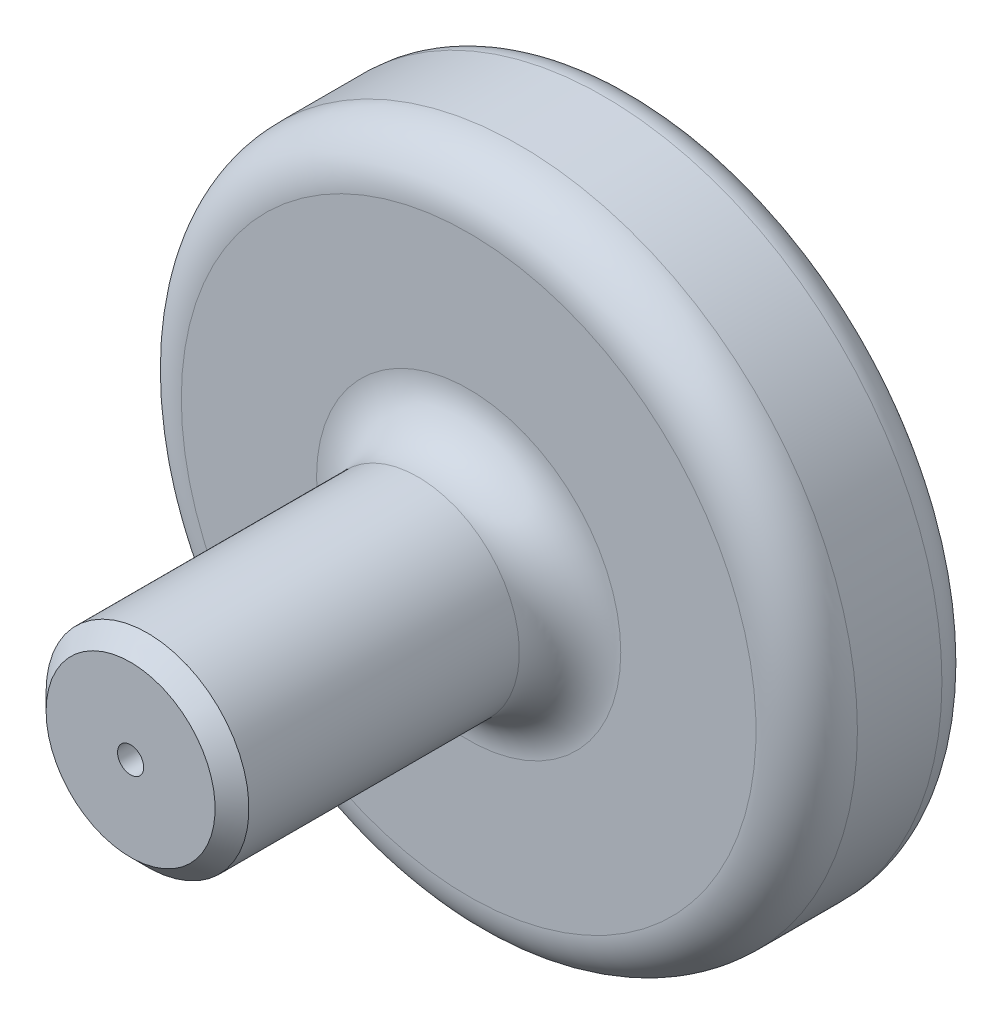
SolidWorks part; units mm, degrees
ref_plane "Front Plane" through (0, 0, 0) normal (0, 0, 1) x (1, 0, 0)
ref_plane "Top Plane" through (0, 0, 0) normal (0, 1, 0) x (1, 0, 0)
ref_plane "Right Plane" through (0, 0, 0) normal (1, 0, 0) x (0, 0, -1)
sketch "Sketch1" plane through (0, 0, 0) normal (0, 1, 0) x (1, 0, 0)
  line L0 (0, 0) -> (100, 0)
  line L1 (100, 0) -> (100, -50)
  line L2 (100, -50) -> (30, -50)
  line L3 (30, -50) -> (30, -150)
  line L4 (30, -150) -> (0, -150)
  line L5 (0, 26.9598) -> (0, -64.4594) construction
  line L6 (0, 0) -> (0, -150)
  dimension "D1" = 100
  dimension "D2" = 50
  dimension "D3" = 30
  dimension "D4" = 150
revolve "Revolve1" add sketch "Sketch1" angle 360 about L5
fillet "Fillet1" radius 10 1 edges at (-100, 0, 0)
chamfer "Chamfer1" distance 5 angle 45 1 edges at (-30, 0, 150)
fillet "Fillet2" radius 15 2 edges at (-30, 0, 50) (-100, 0, 50)
sketch "Sketch2" plane through (0, 0, 150) normal (0, 0, 1) x (1, 0, 0)
  circle A0 centre (0, 0) radius 3.8602
extrude "Cut-Extrude1" cut sketch "Sketch2" against normal through all
sketch "Sketch3" plane through (0, 0, 0) normal (0, 0, -1) x (-1, 0, 0)
  line L0 (0, 0) -> (-47.7221, 0)
  circle A0 centre (0, 0) radius 50
